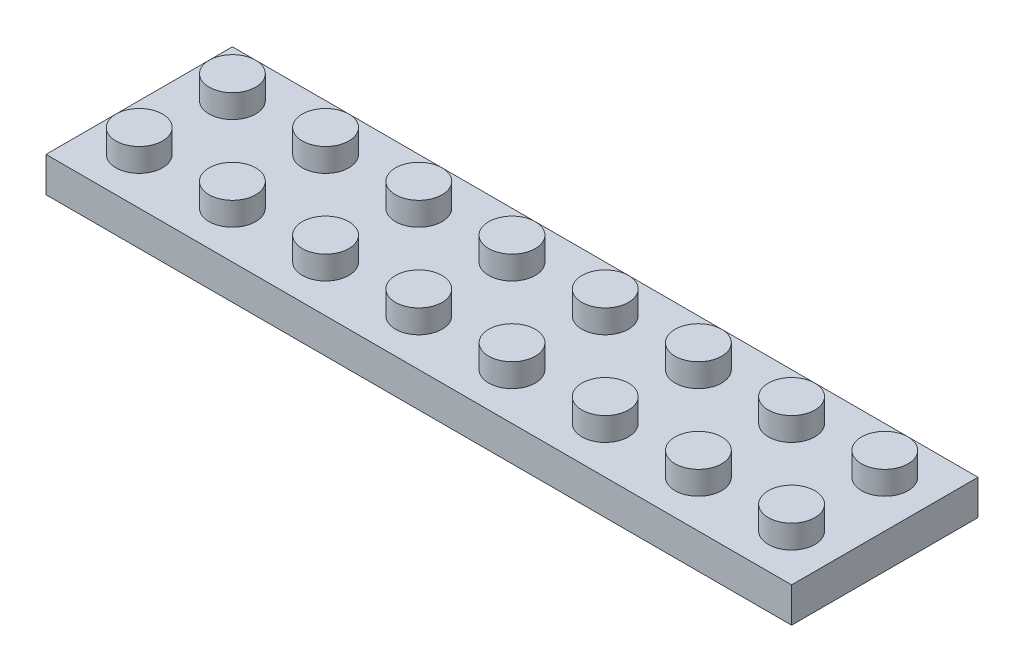
SolidWorks part; units mm, degrees
ref_plane "Front Plane" through (0, 0, 0) normal (0, 0, 1) x (1, 0, 0)
ref_plane "Top Plane" through (0, 0, 0) normal (0, 1, 0) x (1, 0, 0)
ref_plane "Right Plane" through (0, 0, 0) normal (1, 0, 0) x (0, 0, -1)
sketch "Sketch1" plane through (0, 0, 0) normal (0, 1, 0) x (1, 0, 0)
  line L1 (-32, 8) -> (32, 8)
  line L2 (-32, 8) -> (-32, -8)
  line L3 (-32, -8) -> (32, -8)
  line L4 (32, 8) -> (32, -8)
  line L5 (-32, 8) -> (32, -8) construction
  line L6 (-32, -8) -> (32, 8) construction
  point P0 (0, 0)
  dimension "D1" = 64
  dimension "D2" = 16
extrude "Boss-Extrude1" add sketch "Sketch1" along normal blind 3
sketch "Sketch2" plane through (0, 3, 0) normal (0, 1, 0) x (1, 0, 0)
  line L0 (-32, 8) -> (-32, -8) construction
  line L1 (32, 8) -> (-32, 8) construction
  circle A0 centre (-28, 4) radius 2
  circle A1 centre (-20, 4) radius 2
  circle A2 centre (-12, 4) radius 2
  circle A3 centre (-4, 4) radius 2
  circle A4 centre (4, 4) radius 2
  circle A5 centre (12, 4) radius 2
  circle A6 centre (20, 4) radius 2
  circle A7 centre (28, 4) radius 2
  circle A8 centre (-20, -4) radius 2
  circle A9 centre (-12, -4) radius 2
  circle A10 centre (-4, -4) radius 2
  circle A11 centre (4, -4) radius 2
  circle A12 centre (12, -4) radius 2
  circle A13 centre (20, -4) radius 2
  circle A14 centre (28, -4) radius 2
  circle A15 centre (-28, -4) radius 2
  dimension "D1" = 4
  dimension "D2" = 4
  dimension "D3" = 4
  dimension "D4" = 8
  dimension "D5" = 2
extrude "Boss-Extrude2" add sketch "Sketch2" along normal blind 2
shell "Shell1" thickness 1
sketch "Sketch3" plane through (0, 2, 0) normal (0, -1, 0) x (1, 0, 0)
  line L1 (-32, -8) -> (-32, 8) construction
  circle A0 centre (-24, 0) radius 1.8
  circle A1 centre (-24, 0) radius 2.8
  point P3 (0, 0)
  dimension "D1" = 5.6
  dimension "D2" = 3.6
  dimension "D3" = 8
extrude "Boss-Extrude3" add sketch "Sketch3" along normal blind 2
pattern_linear "LPattern1" count 7 spacing 8 along (1, 0, 0) of "Boss-Extrude3"
